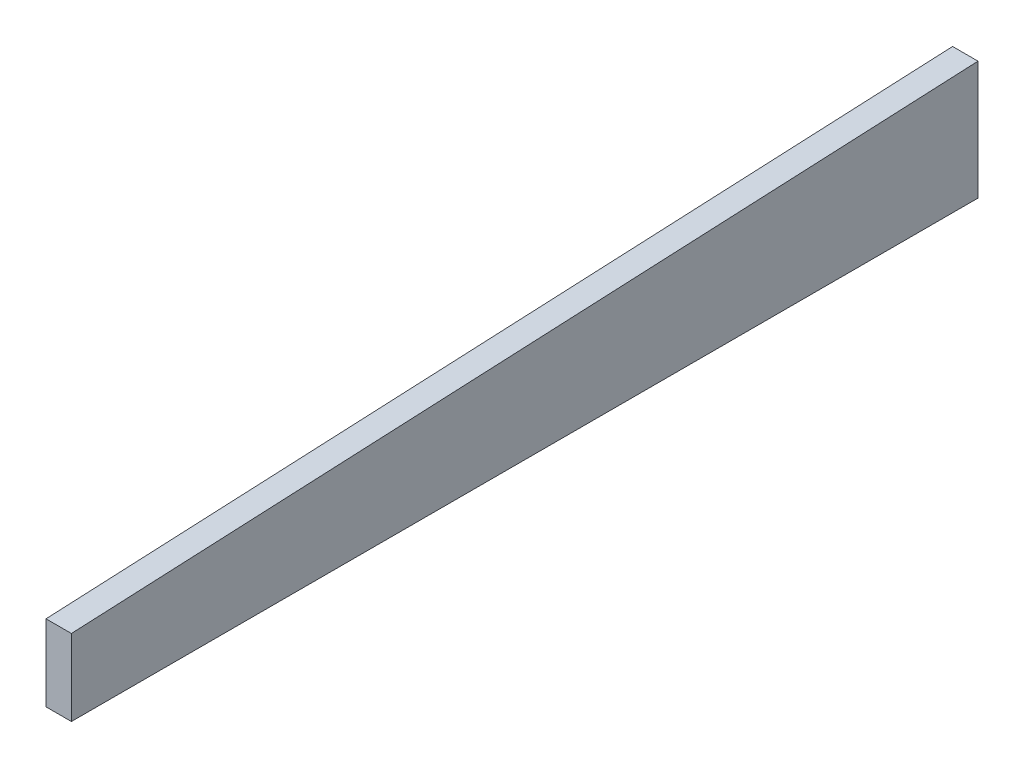
SolidWorks part; units mm, degrees
ref_plane "Front" through (0, 0, 0) normal (0, 0, 1) x (1, 0, 0)
ref_plane "Top" through (0, 0, 0) normal (0, 1, 0) x (1, 0, 0)
ref_plane "Right" through (0, 0, 0) normal (1, 0, 0) x (0, 0, -1)
sketch "Sketch1" plane through (0, 0, 0) normal (1, 0, 0) x (0, 0, -1)
  line L1 (-66.3484, 29.6364) -> (613.1016, 61.3864)
  line L2 (-66.3484, 29.6364) -> (-66.3484, -27.5136)
  line L3 (-66.3484, -27.5136) -> (613.1016, -27.5136)
  line L4 (613.1016, 61.3864) -> (613.1016, -27.5136)
extrude "Extrude1" add sketch "Sketch1" along normal blind 19.05
